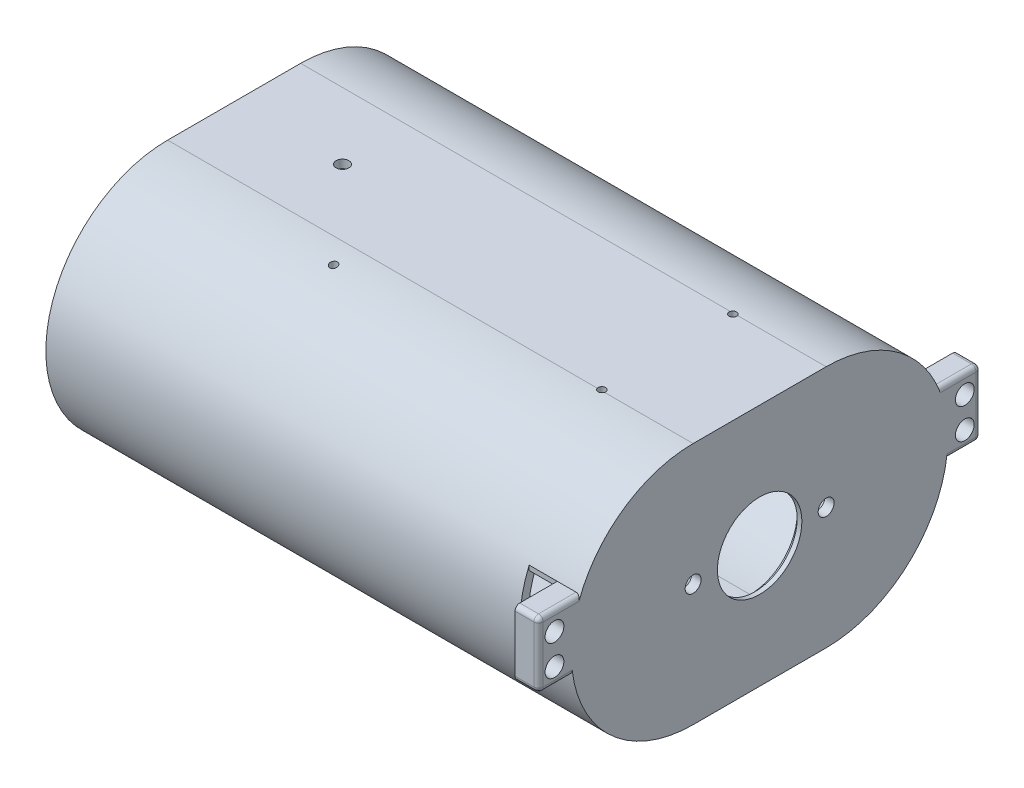
SolidWorks part; units mm, degrees
ref_plane "Front Plane" through (0, 0, 0) normal (0, 0, 1) x (1, 0, 0)
ref_plane "Top Plane" through (0, 0, 0) normal (0, 1, 0) x (1, 0, 0)
ref_plane "Right Plane" through (0, 0, 0) normal (1, 0, 0) x (0, 0, -1)
sketch "Sketch1" plane through (0, 0, 0) normal (1, 0, 0) x (0, 0, -1)
  line L0 (14.176, -14.176) -> (14.176, 14.176)
  line L1 (-28.3521, 0) -> (0, 0)
  line L2 (14.176, 0) -> (0, 0)
  line L3 (-14.176, 0) -> (0, 0)
  line L4 (-14.176, 24.2) -> (14.176, 24.2)
  line L5 (14.176, -24.2) -> (-14.176, -24.2)
  line L6 (-14.176, 25.95) -> (14.176, 25.95)
  line L7 (14.176, -25.95) -> (-14.176, -25.95)
  circle A0 centre (0, 0) radius 10.024 construction
  circle A1 centre (-28.3521, 0) radius 10.024 construction
  circle A2 centre (-14.176, 0) radius 3.0546
  circle A3 centre (14.176, 14.176) radius 10.024 construction
  circle A4 centre (14.176, -14.176) radius 10.024 construction
  circle A5 centre (14.176, 0) radius 3.0546
  arc A6 (-14.176, 24.2) -> (-14.176, -24.2) centre (-14.176, 0) ccw
  arc A7 (14.176, -24.2) -> (14.176, 24.2) centre (14.176, 0) ccw
  arc A8 (14.176, -25.95) -> (14.176, 25.95) centre (14.176, 0) ccw
  arc A9 (-14.176, 25.95) -> (-14.176, -25.95) centre (-14.176, 0) ccw
  circle A10 centre (-28.3521, 0) radius 9.824
  circle A11 centre (0, 0) radius 9.824
  circle A12 centre (14.176, 14.176) radius 9.824
  circle A13 centre (14.176, -14.176) radius 9.824
  dimension "D3" = 0.2
  dimension "D5" = 0.2
  dimension "D4" = 0.2
  dimension "D2" = 1.75
  dimension "D1" = 24.2
  dimension "D6" = 0.2
extrude "Boss-Extrude1" add sketch "Sketch1" against normal blind 110 contours L6 A9 L7 A8 A7 L5 A6 L4
sketch "Sketch5" plane through (0, 0, 0) normal (1, 0, 0) x (0, 0, -1)
  line L0 (14.176, -14.176) -> (14.176, 14.176) construction
  line L1 (-28.3521, 0) -> (0, 0) construction
  line L2 (14.176, 0) -> (0, 0) construction
  line L3 (-14.176, 0) -> (0, 0) construction
  line L4 (-14.176, 24.2) -> (14.176, 24.2)
  line L5 (14.176, -24.2) -> (-14.176, -24.2)
  line L6 (-14.176, 25.95) -> (14.176, 25.95)
  line L7 (14.176, -25.95) -> (-14.176, -25.95)
  line L8 (0, 4.0632) -> (0, -4.2632) construction
  line L9 (11.6656, -4.2632) -> (11.6656, 4.0632) construction
  line L12 (-11.6656, -4.2632) -> (-11.6656, 4.0632) construction
  line L15 (11.6656, 4.0632) -> (-11.6656, 4.0632) construction
  line L16 (0, 0) -> (-11.6656, -4.2632) construction
  line L17 (0, 0) -> (-11.6656, 4.0632) construction
  line L18 (11.6656, -4.2632) -> (-11.6656, -4.2632) construction
  circle A0 centre (0, 0) radius 10.024 construction
  circle A1 centre (-28.3521, 0) radius 10.024 construction
  circle A2 centre (-14.176, 0) radius 1.7
  circle A3 centre (14.176, 14.176) radius 10.024 construction
  circle A4 centre (14.176, -14.176) radius 10.024 construction
  circle A5 centre (14.176, 0) radius 1.7
  arc A6 (-14.176, 24.2) -> (-14.176, -24.2) centre (-14.176, 0) ccw
  arc A7 (14.176, -24.2) -> (14.176, 24.2) centre (14.176, 0) ccw
  arc A8 (14.176, -25.95) -> (14.176, 25.95) centre (14.176, 0) ccw
  arc A9 (-14.176, 25.95) -> (-14.176, -25.95) centre (-14.176, 0) ccw
  circle A10 centre (-28.3521, 0) radius 9.824 construction
  circle A11 centre (0, 0) radius 10.05 construction
  circle A12 centre (14.176, 14.176) radius 9.824 construction
  circle A13 centre (14.176, -14.176) radius 9.824 construction
  arc A14 (7.2294, -7.2294) -> (7.2294, 7.2294) centre (0, 0) ccw construction
  arc A15 (21.1226, -7.2294) -> (21.1226, 7.2294) centre (28.3521, 0) cw construction
  circle A16 centre (0, 0) radius 8.85 construction
  arc A17 (-6.888, -6.888) -> (-21.2297, -6.888) centre (-14.0589, -14.0589) ccw construction
  arc A18 (-6.7123, 6.788) -> (-21.054, 6.788) centre (-13.8831, 13.9589) cw construction
  circle A19 centre (-10.2318, -2.5392) radius 0.75 construction
  circle A20 centre (-10.2318, 2.5392) radius 0.75 construction
  dimension "D3" = 0.2
  dimension "D5" = 0.2
  dimension "D4" = 17.7
  dimension "D2" = 1.75
  dimension "D1" = 24.2
  dimension "D7" = 3.4
  dimension "D9" = 1.5
  dimension "D10" = 2.5392
  dimension "D8" = 10.2318
  dimension "D6" = 0.2
extrude "Boss-Extrude2" add sketch "Sketch5" along normal blind 2 contours L1 A2 | L1 A2 | L2 A5 L0 | L0 A5 L2 | L0 A5 | L3 A16 L2 | L2 A16 L3 | L3 A16 L18 L8 | L15 A16 L3 L8 | A11 L15 L12 L3 A20 | A11 L3 L12 L18 A19 | A16 L1 A11 L18 | A16 L15 A11 L1 | A19 | A20 | L18 A16 L2 L8 | L2 A16 L15 L8 | A16 L2 A11 L15 | A16 L18 A11 L2 | A14 L18 L9 L2 | L2 A14 L15 A11 | L18 A14 L2 A11 | A9 L7 A8 L6
sketch "Sketch6" plane through (2, 0, 0) normal (1, 0, 0) x (0, 0, -1)
  line L1 (-10.9429, -3.7145) -> (10.9429, -3.7145)
  line L2 (-10.9429, -3.7145) -> (-10.9429, 3.7145)
  line L3 (-10.9429, 3.7145) -> (10.9429, 3.7145)
  line L4 (10.9429, -3.7145) -> (10.9429, 3.7145)
  line L5 (-10.9429, -3.7145) -> (10.9429, 3.7145) construction
  line L6 (-10.9429, 3.7145) -> (10.9429, -3.7145) construction
  circle A0 centre (0, 0) radius 9
  dimension "D1" = 18
extrude "Cut-Extrude2" cut sketch "Sketch6" against normal through all contours L1 A0 | L3 A0 L1 | L3 A0
sketch "Sketch7" plane through (0, 25.95, 0) normal (0, 1, 0) x (1, 0, 0)
  circle A2 centre (-86.9078, 0) radius 1.35
  dimension "D1" = 2.7
extrude "Cut-Extrude3" cut sketch "Sketch7" against normal blind 10
sketch "Sketch8" plane through (-81.2, -21.8016, 13.8009) normal (0, -0.8449, 0.5349) x (0, -0.5349, -0.8449)
  circle A1 centre (-11.8517, -5.7078) radius 1.35
  dimension "D1" = 2.7
extrude "Cut-Extrude4" cut sketch "Sketch8" along normal blind 18
sketch "Sketch9" plane through (-81.2, -20.4159, -18.9193) normal (0, -0.7335, -0.6797) x (0, 0.6797, -0.7335)
  circle A0 centre (10.2883, -5.7078) radius 0.9 construction
  circle A1 centre (10.2883, -5.7078) radius 0.9 construction
  circle A2 centre (10.2883, -5.7078) radius 1.35
  dimension "D1" = 2.7
extrude "Cut-Extrude5" cut sketch "Sketch9" along normal blind 20
chamfer "Chamfer3" distance 1 angle 45 1 edges at (0, 0, -9)
sketch "Sketch11" plane through (-110, 0, 0) normal (-1, 0, 0) x (0, 0, 1)
  line L0 (34.47, 12.05) -> (35.47, 12.05)
  line L1 (-37.127, 5.7181) -> (-37.6908, 5.7181)
  line L2 (-37.127, 5.7181) -> (-37.127, 6.2819)
  line L3 (-37.127, 6.2819) -> (-37.6908, 6.2819)
  line L4 (-37.6908, 5.7181) -> (-37.6908, 6.2819)
  line L5 (-37.127, 5.7181) -> (-37.6908, 6.2819) construction
  line L6 (-37.127, 6.2819) -> (-37.6908, 5.7181) construction
  line L7 (34.47, 12.05) -> (35.47, 12.05)
  line L8 (34.47, 12.05) -> (34.47, 13.05)
  line L9 (34.47, 13.05) -> (35.47, 13.05)
  line L10 (35.47, 12.05) -> (35.47, 13.05)
  line L11 (34.47, 12.05) -> (35.47, 13.05) construction
  line L12 (34.47, 13.05) -> (35.47, 12.05) construction
  line L13 (34.47, 12.05) -> (34.47, 10.9108)
  line L14 (35.47, 12.05) -> (35.47, 10.9108)
  line L15 (34.47, 10.9108) -> (35.47, 10.9108)
  arc A0 (-14.176, 24.2) -> (-14.176, -24.2) centre (-14.176, 0) ccw construction
  point P0 (-37.4089, 6)
  point P6 (34.97, 12.55)
  arc M21 (14.176, 24.2) -> (14.176, -24.2) centre (14.176, 0) cw
  dimension "D1" = 1
extrude "Cut-Extrude6" cut sketch "Sketch11" against normal blind 30 contours L9 L8 L0 M21 | L0 L10 L9 M21 | L14 L0 M21 | L13 L15 L14 L0 M21
sketch "Sketch17" plane through (0, 25.95, 0) normal (0, 1, 0) x (1, 0, 0)
  line L0 (-83.7582, -21.55) -> (-19.8585, -21.55) construction
  line L1 (-19.8585, -21.55) -> (-15.1582, -16.8498) construction
  line L2 (-15.1582, -16.8498) -> (-15.1582, 16.45) construction
  line L3 (-15.1582, 16.45) -> (-17.6582, 18.95) construction
  line L4 (-17.6582, 18.95) -> (-17.6582, 31.75) construction
  line L5 (-17.6582, 31.75) -> (-83.7582, 31.75) construction
  line L6 (-83.7582, 31.75) -> (-83.7582, -21.55) construction
  line L7 (-17.6582, 13.95) -> (-17.6582, 14.176)
  line L8 (-110, 14.176) -> (2, 14.176) construction
  line L9 (-17.6582, -13.95) -> (-17.6582, -14.176)
  line L10 (-110, -14.176) -> (2, -14.176) construction
  circle A0 centre (-68.4582, 29.15) radius 0.8
  circle A1 centre (-17.6582, 13.95) radius 0.8
  circle A2 centre (-17.6582, -13.95) radius 0.8
  circle A3 centre (-69.7582, -19.05) radius 0.8
  dimension "D2" = 48.2
  dimension "D15" = 1.6
  dimension "D1" = 27.9
  dimension "D3" = 66.1
  dimension "D4" = 68.6
  dimension "D5" = 53.3
  dimension "D6" = 50.8
  dimension "D7" = 52.1
  dimension "D8" = 2.6
  dimension "D9" = 15.2
  dimension "D10" = 2.5
  dimension "D11" = 135
  dimension "D12" = 225
  dimension "D13" = 2.5
  dimension "D14" = 7.6
  dimension "D16" = 4.7002
  dimension "D17" = 12.8
extrude "Cut-Extrude11" cut sketch "Sketch17" against normal blind 10
ref_plane "Plane1" through (0, 0, -40.126) normal (0, 0, -1) x (-1, 0, 0)
sketch "Sketch19" plane through (0, 0, -40.126) normal (0, 0, -1) x (-1, 0, 0)
  line L1 (3, -10) -> (9, -10)
  line L2 (3, -10) -> (3, 10)
  line L3 (3, 10) -> (9, 10)
  line L4 (9, -10) -> (9, 10)
  line L5 (3, -10) -> (9, 10) construction
  line L6 (3, 10) -> (9, -10) construction
  line L8 (-2, 25.95) -> (-2, -25.95) construction
  point P0 (6, 0)
  dimension "D1" = 20
  dimension "D2" = 6
  dimension "D3" = 5
extrude "Cut-Extrude12" cut sketch "Sketch19" against normal blind 2
mirror "Mirror1" about plane through (0, 0, 0) normal (0, 0, 1) of "Cut-Extrude12"
sketch "Sketch20" plane through (-3, 0, 0) normal (-1, 0, 0) x (0, 0, 1)
  line L0 (-38.126, -3.4695) -> (-38.126, -9.99) construction
  line L1 (-38.126, -4.01) -> (-46.126, -4.01)
  line L2 (-38.126, -4.01) -> (-38.126, 9.99)
  line L3 (-38.126, 9.99) -> (-46.126, 9.99)
  line L4 (-47.126, -3.01) -> (-47.126, 8.99)
  line L7 (-42.726, -0.4695) -> (-44.726, -0.4695) construction
  line L8 (-42.726, -1.4695) -> (-44.726, -1.4695)
  line L9 (-42.726, 0.5305) -> (-44.726, 0.5305)
  line L10 (-42.726, 6.0305) -> (-44.726, 6.0305) construction
  line L11 (-42.726, 5.0305) -> (-44.726, 5.0305)
  line L12 (-42.726, 7.0305) -> (-44.726, 7.0305)
  circle A0 centre (-43.726, -0.4695) radius 1 construction
  arc A1 (-42.726, -1.4695) -> (-42.726, 0.5305) centre (-42.726, -0.4695) ccw
  arc A2 (-44.726, 0.5305) -> (-44.726, -1.4695) centre (-44.726, -0.4695) ccw
  circle A3 centre (-43.726, 6.0305) radius 1 construction
  arc A4 (-42.726, 5.0305) -> (-42.726, 7.0305) centre (-42.726, 6.0305) ccw
  arc A5 (-44.726, 7.0305) -> (-44.726, 5.0305) centre (-44.726, 6.0305) ccw
  arc A6 (-47.126, -3.01) -> (-46.126, -4.01) centre (-46.126, -3.01) ccw
  arc A7 (-46.126, 9.99) -> (-47.126, 8.99) centre (-46.126, 8.99) ccw
  circle A8 centre (-43.726, 6.0305) radius 2
  circle A9 centre (-43.726, -0.4695) radius 2
  point P1 (-47.126, 9.99)
  point P3 (-47.126, -4.01)
  point P16 (-43.726, -0.4695)
  point P26 (-43.726, 6.0305)
  arc M5 (-38.126, 9.99) -> (-38.126, -9.99) centre (-14.176, 0) ccw
  dimension "D4" = 2
  dimension "D1" = 14
  dimension "D2" = 9
  dimension "D3" = 2
extrude "Boss-Extrude3" add sketch "Sketch20" against normal blind 5 contours L3 A7 L4 A6 L1 A9 A8 M5
fillet "Fillet1" radius 1 5 edges at (2, -4.01, -42.9702) (2, -3.7171, -46.8331) (2, 9.99, -42.126) (2, 9.6971, -46.8331) (2, 2.99, -47.126)
mirror "Mirror2" about plane through (0, 0, 0) normal (0, 0, 1) of "Boss-Extrude3", "Fillet1"
sketch "Sketch21" plane through (-3, 0, 0) normal (-1, 0, 0) x (0, 0, 1)
  line L0 (-39.8143, -4.01) -> (-38.126, -4.01)
  line L1 (-38.126, -3.4695) -> (-38.126, -9.99) construction
  line L2 (-38.126, -4.01) -> (-38.126, -9.99)
  line L3 (38.126, -3.4695) -> (38.126, -9.99) construction
  line L4 (38.126, -4.01) -> (38.126, -9.99)
  line L5 (39.8143, -4.01) -> (38.126, -4.01)
  arc A0 (-39.8143, -4.01) -> (-38.126, -9.99) centre (-14.176, 0) ccw construction
  arc A1 (-39.8143, -4.01) -> (-38.126, -9.99) centre (-14.176, 0) ccw
  arc A2 (38.126, -9.99) -> (39.8143, -4.01) centre (14.176, 0) ccw construction
  arc A3 (38.126, -9.99) -> (39.8143, -4.01) centre (14.176, 0) ccw
extrude "Boss-Extrude4" add sketch "Sketch21" along normal up to surface (6 mm away) up to face at (-9, 0, 38.6885)
sketch "Sketch22" plane through (0, 0, -38.126) normal (0, 0, -1) x (-1, 0, 0)
  line L0 (9, 3.4695) -> (9, 9.99) construction
  line L1 (3, 3.4695) -> (9, 3.4695)
  line L2 (3, 3.4695) -> (3, 8.99)
  line L3 (3, 8.99) -> (9, 8.99)
  line L4 (9, 3.4695) -> (9, 8.99)
  line L6 (9, 9.99) -> (3, 9.99) construction
  dimension "D1" = 1
extrude "Cut-Extrude13" cut sketch "Sketch22" against normal through all
